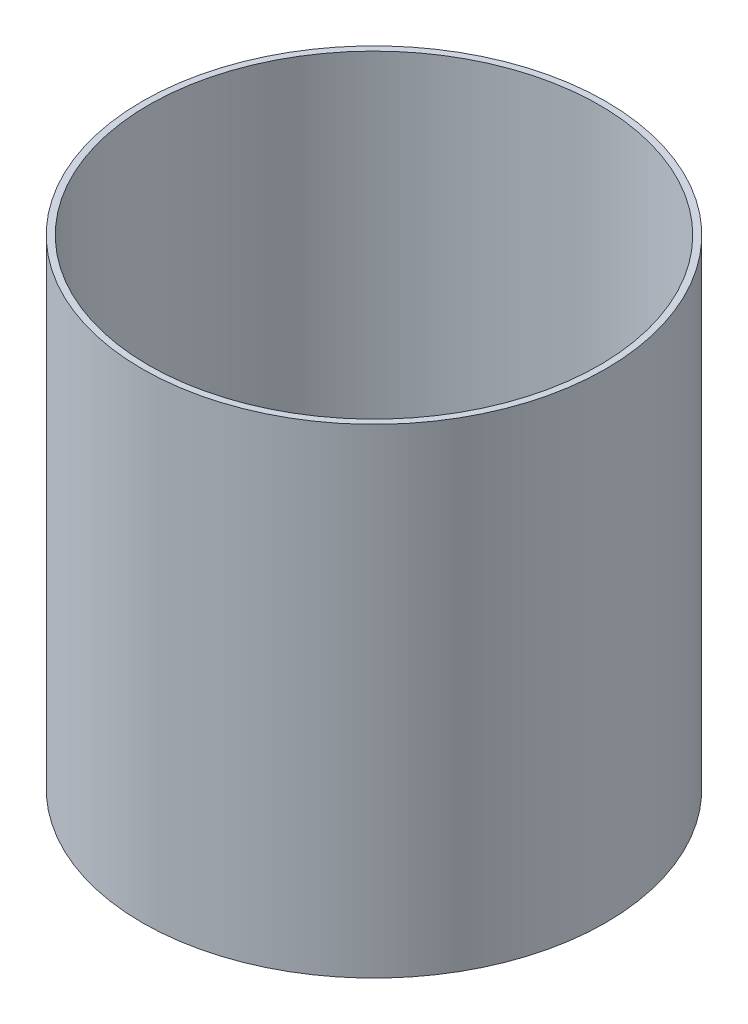
SolidWorks part; units mm, degrees
material "Glass"
ref_plane "Front Plane" through (0, 0, 0) normal (0, 0, 1) x (1, 0, 0)
ref_plane "Top Plane" through (0, 0, 0) normal (0, 1, 0) x (1, 0, 0)
ref_plane "Right Plane" through (0, 0, 0) normal (1, 0, 0) x (0, 0, -1)
sketch "Sketch1" plane through (0, 0, 0) normal (0, 1, 0) x (1, 0, 0)
  circle A0 centre (0, 0) radius 141
  circle A1 centre (0, 0) radius 145
  dimension "D1" = 282
  dimension "D2" = 290
extrude "Boss-Extrude1" add sketch "Sketch1" against normal blind 300
